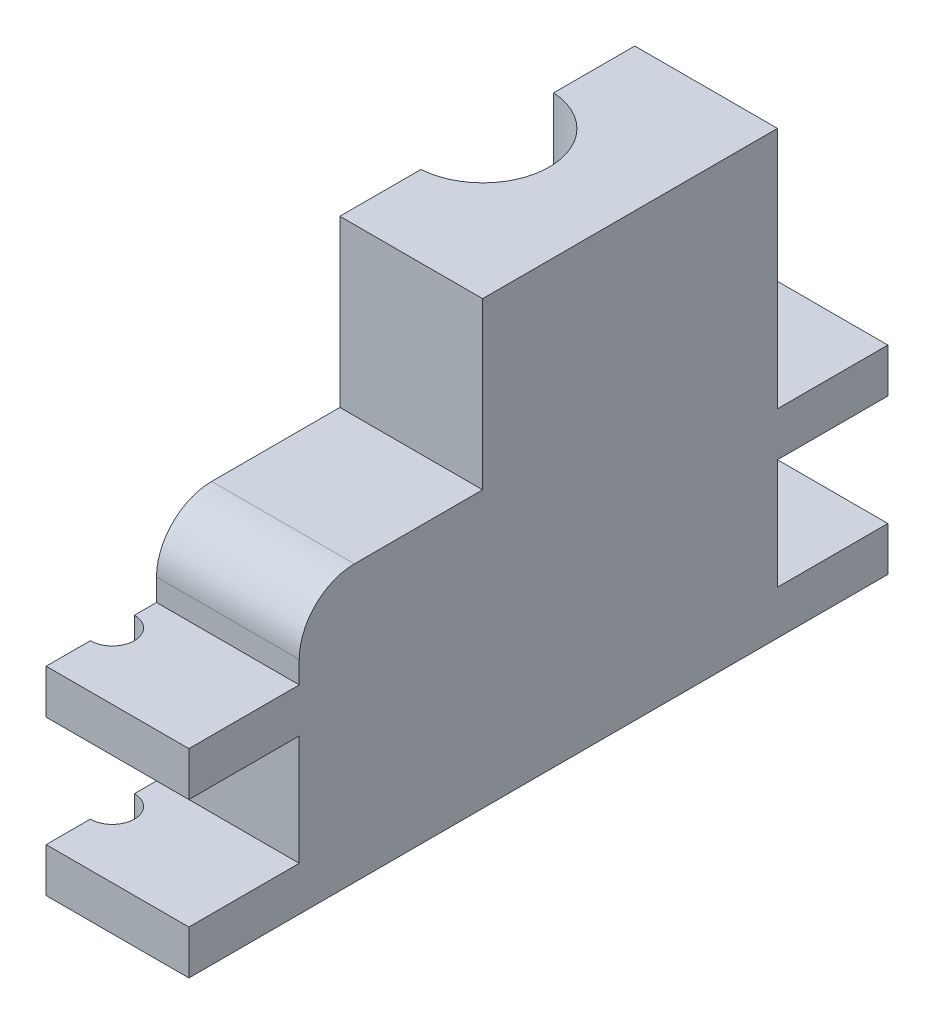
SolidWorks part; units mm, degrees
ref_plane "Front Plane" through (0, 0, 0) normal (0, 0, 1) x (1, 0, 0)
ref_plane "Top Plane" through (0, 0, 0) normal (0, 1, 0) x (1, 0, 0)
ref_plane "Right Plane" through (0, 0, 0) normal (1, 0, 0) x (0, 0, -1)
sketch "Sketch1" plane through (0, 0, 0) normal (0, 1, 0) x (1, 0, 0)
  line L0 (0, 0) -> (0, 45.6184)
  line L1 (0, 68.58) -> (0, 82.55)
  line L2 (0, 82.55) -> (25.4, 82.55)
  line L3 (25.4, 82.55) -> (25.4, 0)
  line L4 (25.4, 0) -> (0, 0)
  arc A0 (0, 45.6184) -> (0, 68.58) centre (0, 57.0992) ccw
  dimension "D1" = 11.4808
  dimension "D2" = 25.4
  dimension "D3" = 13.97
  dimension "D4" = 82.55
extrude "Boss-Extrude1" add sketch "Sketch1" along normal blind 76.2
sketch "Sketch2" plane through (0, 0, 0) normal (0, -1, 0) x (1, 0, 0)
  circle A0 centre (0, -57.0992) radius 15.24
  dimension "D1" = 30.48
extrude "Cut-Extrude1" cut sketch "Sketch2" against normal blind 38.1
ref_plane "Plane1" through (0, 16.51, 0) normal (0, -1, 0) x (-1, 0, 0)
sketch "Sketch3" plane through (0, 16.51, 0) normal (0, -1, 0) x (-1, 0, 0)
  circle A0 centre (0, 57.0992) radius 17.78
  arc A1 (0, 68.58) -> (0, 45.6184) centre (0, 57.0992) ccw construction
  arc A2 (0, 68.58) -> (0, 45.6184) centre (0, 57.0992) ccw
  dimension "D1" = 35.56
extrude "Cut-Extrude2" cut sketch "Sketch3" against normal blind 6.35 contours A0
sketch "Sketch4" plane through (0, 0, 0) normal (-1, 0, 0) x (0, 0, 1)
  line L0 (-41.8592, 38.1) -> (-45.6184, 38.1) construction
  line L1 (-57.0992, 0) -> (-12.6492, 0)
  line L2 (-57.0992, 0) -> (-57.0992, 38.1)
  line L3 (-57.0992, 38.1) -> (-35.5092, 38.1)
  line L4 (-12.6492, 0) -> (-12.6492, 15.24)
  line L5 (-72.3392, 0) -> (-41.8592, 0) construction
  arc A0 (-12.6492, 15.24) -> (-35.5092, 38.1) centre (-35.5092, 15.24) ccw
  dimension "D2" = 22.86
  dimension "D1" = 44.45
extrude "Cut-Extrude3" cut sketch "Sketch4" against normal blind 12.7
sketch "Sketch5" plane through (25.4, 0, 0) normal (1, 0, 0) x (0, 0, -1)
  line L1 (0, 76.2) -> (31.6484, 76.2)
  line L2 (0, 76.2) -> (0, 38.1)
  line L3 (31.6484, 47.625) -> (9.525, 47.625)
  line L4 (31.6484, 76.2) -> (31.6484, 47.625)
  line L5 (45.6184, 76.2) -> (45.6184, 38.1) construction
  line L6 (0, 76.2) -> (0, 0) construction
  arc A0 (9.525, 47.625) -> (0, 38.1) centre (9.525, 38.1) ccw
  dimension "D1" = 9.525
  dimension "D2" = 13.97
extrude "Cut-Extrude4" cut sketch "Sketch5" against normal through all
sketch "Sketch6" plane through (0, 0, 0) normal (-1, 0, 0) x (0, 0, 1)
  line L1 (-82.55, 76.2) -> (0, 76.2)
  line L2 (-82.55, 76.2) -> (-82.55, 0)
  line L3 (-82.55, 0) -> (0, 0)
  line L4 (0, 76.2) -> (0, 0)
  point P4 (-105.0167, 105.0167)
  point P6 (0, 0)
  point P10 (0, 0)
extrude "Cut-Extrude5" cut sketch "Sketch6" against normal blind 0.762 contours L1 L4 L3 L2
sketch "Sketch9" plane through (0, 0, 0) normal (0, -1, 0) x (1, 0, 0)
  line L0 (25.4, 0) -> (25.4, -82.55) construction
  line L1 (0.762, -12.6492) -> (25.4, -12.6492)
  line L2 (0.762, -12.6492) -> (0.762, 3.81)
  line L3 (0.762, 19.05) -> (25.4, 19.05)
  line L4 (25.4, -12.6492) -> (25.4, 19.05)
  line L5 (0.762, -72.3201) -> (25.4, -72.3201)
  line L6 (0.762, -72.3201) -> (0.762, -86.36)
  line L7 (0.762, -101.6) -> (25.4, -101.6)
  line L8 (25.4, -72.3201) -> (25.4, -101.6)
  line L9 (0.762, 0) -> (25.4, 0) construction
  line L10 (25.4, -82.55) -> (0.762, -82.55) construction
  line L11 (0.762, -93.98) -> (0.762, -101.6)
  line L12 (0.762, 11.43) -> (0.762, 19.05)
  arc A0 (0.762, -93.98) -> (0.762, -86.36) centre (0.762, -90.17) ccw
  arc A1 (0.762, 3.81) -> (0.762, 11.43) centre (0.762, 7.62) ccw
  dimension "D3" = 7.62
  dimension "D5" = 7.62
  dimension "D1" = 19.05
  dimension "D2" = 19.05
  dimension "D4" = 7.62
  dimension "D6" = 7.62
extrude "Boss-Extrude2" add sketch "Sketch9" against normal blind 7.62
pattern_linear "LPattern1" count 2 spacing 26.67 along (0, 1, 0) of "Boss-Extrude2"
